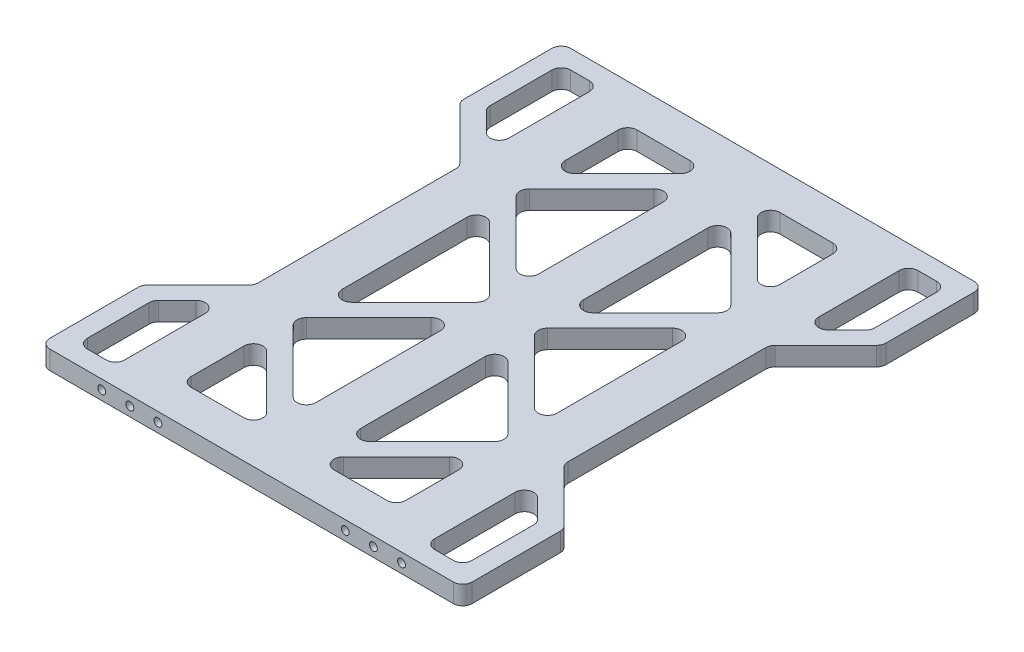
SolidWorks part; units mm, degrees
material "1060 Alloy"
ref_plane "Front Plane" through (0, 0, 0) normal (0, 0, 1) x (1, 0, 0)
ref_plane "Top Plane" through (0, 0, 0) normal (0, 1, 0) x (1, 0, 0)
ref_plane "Right Plane" through (0, 0, 0) normal (1, 0, 0) x (0, 0, -1)
sketch "Sketch1" plane through (0, 0, 0) normal (0, 1, 0) x (1, 0, 0)
  line L0 (0, 139) -> (0, 0) construction
  line L1 (0, 0) -> (82.7, 0) construction
  line L2 (-112.7, 139) -> (112.7, 139)
  line L3 (112.7, 139) -> (112.7, 84.8579)
  line L4 (112.7, 84.8579) -> (82.7, 54.8579)
  line L5 (82.7, 54.8579) -> (82.7, -54.8579)
  line L6 (112.7, -84.8579) -> (82.7, -54.8579)
  line L7 (112.7, -139) -> (112.7, -84.8579)
  line L8 (-112.7, -139) -> (112.7, -139)
  line L9 (11.9421, 104.8579) -> (57.3, 59.5)
  line L10 (57.3, 59.5) -> (11.9421, 14.1421)
  line L11 (11.9421, 119) -> (57.3, 119)
  line L12 (57.3, 119) -> (57.3, 73.6421)
  line L13 (57.3, 73.6421) -> (11.9421, 119)
  line L14 (82.7, 129) -> (102.7, 129)
  line L15 (102.7, 129) -> (102.7, 89)
  line L16 (102.7, 89) -> (82.7, 69)
  line L17 (82.7, 69) -> (82.7, 129)
  line L18 (11.9421, 14.1421) -> (11.9421, 104.8579)
  line L19 (57.3, 45.3579) -> (11.9421, 0)
  line L20 (57.3, 45.3579) -> (57.3, -45.3579)
  line L21 (11.9421, 119) -> (11.9421, 104.8579) construction
  line L22 (11.9421, 14.1421) -> (11.9421, 0) construction
  line L23 (102.7, -89) -> (82.7, -69)
  line L24 (82.7, -129) -> (102.7, -129)
  line L25 (82.7, -69) -> (82.7, -129)
  line L26 (102.7, -129) -> (102.7, -89)
  line L27 (57.3, -45.3579) -> (11.9421, 0)
  line L28 (57.3, -59.5) -> (11.9421, -14.1421)
  line L29 (11.9421, -104.8579) -> (57.3, -59.5)
  line L30 (11.9421, -14.1421) -> (11.9421, -104.8579)
  line L31 (57.3, -119) -> (57.3, -73.6421)
  line L32 (57.3, -73.6421) -> (11.9421, -119)
  line L33 (11.9421, -119) -> (57.3, -119)
  line L34 (-11.9421, 14.1421) -> (-11.9421, 0) construction
  line L35 (-11.9421, 119) -> (-11.9421, 104.8579) construction
  line L36 (-11.9421, -119) -> (-57.3, -119)
  line L37 (-57.3, -73.6421) -> (-11.9421, -119)
  line L38 (-57.3, -119) -> (-57.3, -73.6421)
  line L39 (-11.9421, -14.1421) -> (-11.9421, -104.8579)
  line L40 (-11.9421, -104.8579) -> (-57.3, -59.5)
  line L41 (-57.3, -59.5) -> (-11.9421, -14.1421)
  line L42 (-57.3, -45.3579) -> (-11.9421, 0)
  line L43 (-102.7, -129) -> (-102.7, -89)
  line L44 (-82.7, -69) -> (-82.7, -129)
  line L45 (-82.7, -129) -> (-102.7, -129)
  line L46 (-102.7, -89) -> (-82.7, -69)
  line L47 (-57.3, 45.3579) -> (-57.3, -45.3579)
  line L48 (-57.3, 45.3579) -> (-11.9421, 0)
  line L49 (-11.9421, 14.1421) -> (-11.9421, 104.8579)
  line L50 (-82.7, 69) -> (-82.7, 129)
  line L51 (-102.7, 89) -> (-82.7, 69)
  line L52 (-102.7, 129) -> (-102.7, 89)
  line L53 (-82.7, 129) -> (-102.7, 129)
  line L54 (-57.3, 73.6421) -> (-11.9421, 119)
  line L55 (-57.3, 119) -> (-57.3, 73.6421)
  line L56 (-11.9421, 119) -> (-57.3, 119)
  line L57 (-57.3, 59.5) -> (-11.9421, 14.1421)
  line L58 (-11.9421, 104.8579) -> (-57.3, 59.5)
  line L59 (-112.7, -139) -> (-112.7, -84.8579)
  line L60 (-112.7, -84.8579) -> (-82.7, -54.8579)
  line L61 (-82.7, 54.8579) -> (-82.7, -54.8579)
  line L62 (-112.7, 84.8579) -> (-82.7, 54.8579)
  line L63 (-112.7, 139) -> (-112.7, 84.8579)
  line L64 (-57.3, 0) -> (-82.7, 0) construction
  line L65 (-70, -161.9996) -> (-70, 161.9996) construction
  point P29 (57.3, 0)
  point P60 (0, -139)
  point P65 (-57.3, 0)
  point P68 (-70, 0)
  dimension "D1" = 278
  dimension "D2" = 30
  dimension "D3" = 10
  dimension "D4" = 10
  dimension "D5" = 10
  dimension "D6" = 20
  dimension "D7" = 25.4
  dimension "D8" = 10
  dimension "D9" = 45
  dimension "D11" = 45
  dimension "D12" = 40
  dimension "D10" = 70
extrude "Boss-Extrude1" add sketch "Sketch1" along normal mid plane 10
fillet "Fillet1" radius 5 58 edges at (-102.7, 0, 129) (-82.7, 0, 129) (-102.7, 0, 89) (-82.7, 0, 69) (-112.7, 0, 139) (-112.7, 0, 84.8579) (-82.7, 0, 54.8579) (-112.7, 0, -139) (-112.7, 0, -84.8579) (-82.7, 0, -54.8579) (-11.9421, 0, 119) (-57.3, 0, 73.6421) (-57.3, 0, 119) (-11.9421, 0, 104.8579) (-11.9421, 0, 14.1421) (-57.3, 0, 59.5) (57.3, 0, 73.6421) (11.9421, 0, 119) (57.3, 0, 119) (57.3, 0, 59.5) (11.9421, 0, 104.8579) (11.9421, 0, 14.1421) (57.3, 0, 45.3579) (57.3, 0, -45.3579) (11.9421, 0, 0) (11.9421, 0, -14.1421) (11.9421, 0, -104.8579) (57.3, 0, -59.5) (57.3, 0, -73.6421) (11.9421, 0, -119) (57.3, 0, -119) (-11.9421, 0, -119) (-57.3, 0, -119) (-57.3, 0, -73.6421) (-57.3, 0, 45.3579) (-11.9421, 0, 0) (-11.9421, 0, -14.1421) (-11.9421, 0, -104.8579) (-57.3, 0, -59.5) (-57.3, 0, -45.3579) (112.7, 0, -139) (82.7, 0, -54.8579) (112.7, 0, -84.8579) (82.7, 0, 54.8579) (112.7, 0, 84.8579) (112.7, 0, 139) (82.7, 0, 69) (102.7, 0, 89) (82.7, 0, 129) (102.7, 0, 129) (102.7, 0, -89) (102.7, 0, -129) (82.7, 0, -129) (82.7, 0, -69) (-102.7, 0, -89) (-102.7, 0, -129) (-82.7, 0, -69) (-82.7, 0, -129)
sketch "Sketch2" plane through (0, 0, 0) normal (0, 0, 1) x (1, 0, 0)
  line L0 (0, 5) -> (0, -5) construction
  line L1 (107.7, 5) -> (-107.7, 5) construction
  line L2 (107.7, -5) -> (-107.7, -5) construction
  line L3 (-50, 0) -> (-80, 0) construction
  point P9 (-65, 0)
  point P10 (-50, 0)
  point P11 (80, 0)
  point P12 (-80, 0)
  point P13 (65, 0)
  point P14 (50, 0)
  dimension "D1" = 15
  dimension "D2" = 50
hole_wizard "M5x0.8 Tapped Hole1" positions "Sketch3" profile "Sketch5" tap size "M5x0.8" standard "ANSI Metric"
sketch "Sketch3" plane through (0, 0, -139) normal (0, 0, -1) x (-1, 0, 0)
  point P0 (-80, 0)
  point P3 (-65, 0)
  point P6 (-50, 0)
  point P9 (50, 0)
  point P12 (65, 0)
  point P15 (80, 0)
sketch "Sketch5" plane through (80, 0, -139) normal (1, 0, 0) x (0, 1, 0)
  line L0 (0, 0) -> (0, 13.6618)
  line L1 (0, 13.6618) -> (2.1, 12.4)
  line L2 (2.1, 12.4) -> (2.1, 0)
  line L5 (2.1, 0) -> (0, 0)
  line L10 (0, 13.6618) -> (-2.1, 12.4) construction
  line L11 (0, -6.35) -> (0, 107.95) construction
  dimension "Tap Drill Dia." = 4.2
  dimension "Tap Drill Depth" = 12.4
  dimension "Drill Angle" = 118
cosmetic thread "Hole Thread1" parameters "D1"=10, "D2"=5
cosmetic thread "Hole Thread2" parameters "D1"=10, "D2"=5
cosmetic thread "Hole Thread3" parameters "D1"=10, "D2"=5
cosmetic thread "Hole Thread4" parameters "D1"=10, "D2"=5
cosmetic thread "Hole Thread5" parameters "D1"=10, "D2"=5
cosmetic thread "Hole Thread6" parameters "D1"=10, "D2"=5
mirror "Mirror1" about plane through (0, 0, 0) normal (0, 0, 1) of "M5x0.8 Tapped Hole1"
equation "\"D1@Sketch1\"=298.00 - 20"
equation "\"D10@Sketch1\"=108.43mm - 8.43 - 30"
